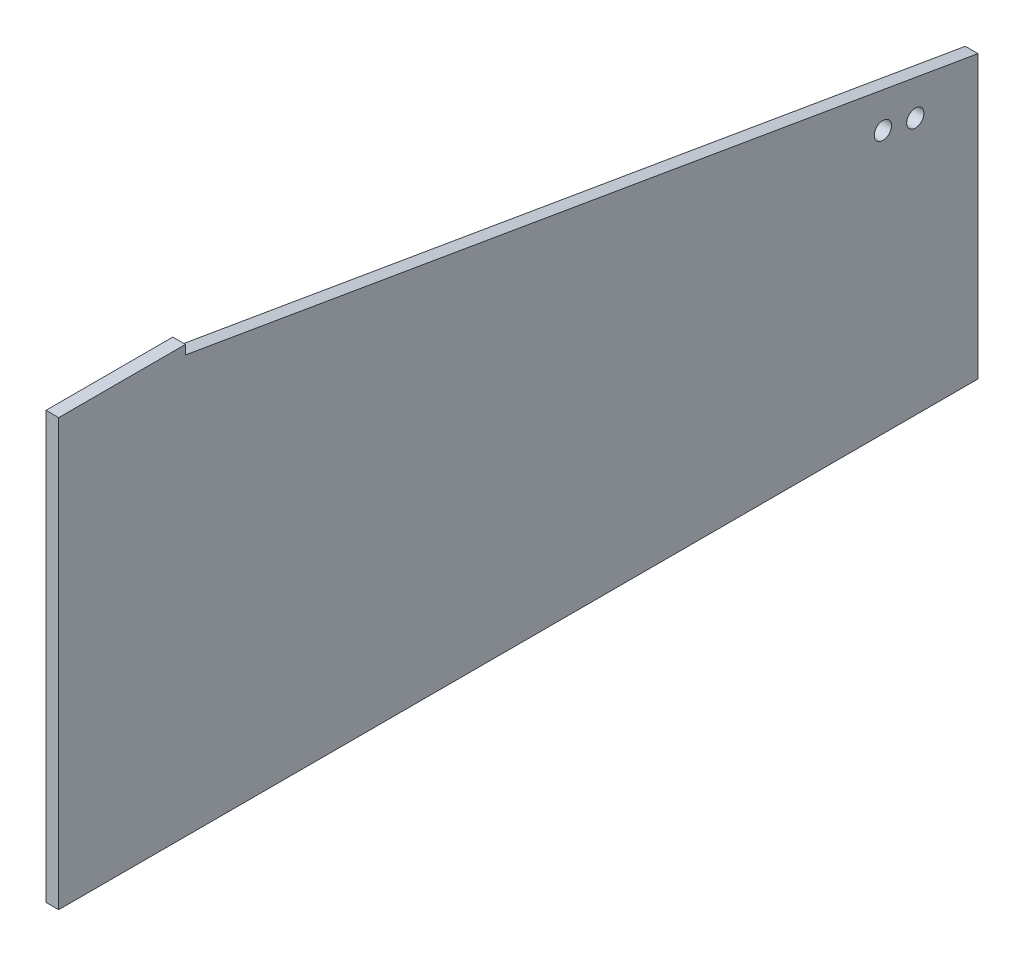
SolidWorks part; units mm, degrees
ref_plane "Front Plane" through (0, 0, 0) normal (0, 0, 1) x (1, 0, 0)
ref_plane "Top Plane" through (0, 0, 0) normal (0, 1, 0) x (1, 0, 0)
ref_plane "Right Plane" through (0, 0, 0) normal (1, 0, 0) x (0, 0, -1)
sketch "Sketch1" plane through (0, 0, 0) normal (1, 0, 0) x (0, 0, -1)
  line L0 (0, 0) -> (0, 605)
  line L1 (0, 605) -> (180, 605)
  line L2 (180, 605) -> (180, 592)
  line L3 (180, 592) -> (1305, 400)
  line L4 (1305, 400) -> (1305, 0)
  line L5 (1305, 0) -> (0, 0)
  line L6 (1170, 373.04) -> (1170, 574.689) construction
  line L7 (1216, 365.1893) -> (1216, 600.6422) construction
  circle A0 centre (1216, 365.1893) radius 12.25
  circle A2 centre (1170, 373.04) radius 12.25
  point P11 (1170, 423.04)
  point P14 (1216, 415.1893)
  dimension "D6" = 89
  dimension "D7" = 24.5
  dimension "D8" = 24.5
  dimension "D9" = 24.5
  dimension "D10" = 135
  dimension "D11" = 50
  dimension "D1" = 605
  dimension "D2" = 180
  dimension "D3" = 13
  dimension "D4" = 1305
  dimension "D5" = 400
  dimension "D12" = 50
extrude "Boss-Extrude1" add sketch "Sketch1" along normal blind 18
